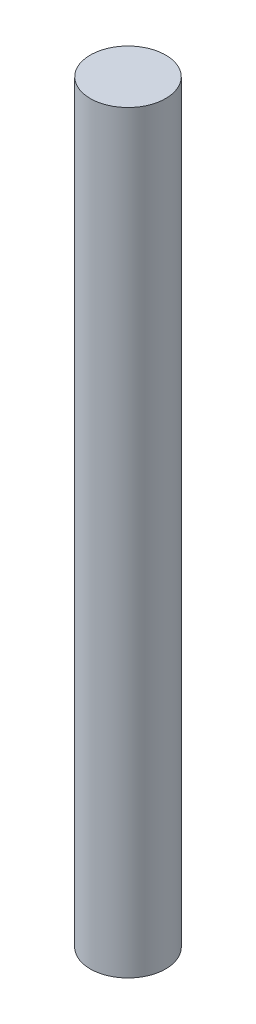
SolidWorks part; units mm, degrees
ref_plane "Front Plane" through (0, 0, 0) normal (0, 0, 1) x (1, 0, 0)
ref_plane "Top Plane" through (0, 0, 0) normal (0, 1, 0) x (1, 0, 0)
ref_plane "Right Plane" through (0, 0, 0) normal (1, 0, 0) x (0, 0, -1)
sketch "Sketch1" plane through (0, 0, 0) normal (0, 1, 0) x (1, 0, 0)
  circle A0 centre (0, 0) radius 2.5
  dimension "D1" = 5
extrude "Boss-Extrude1" add sketch "Sketch1" along normal blind 50
